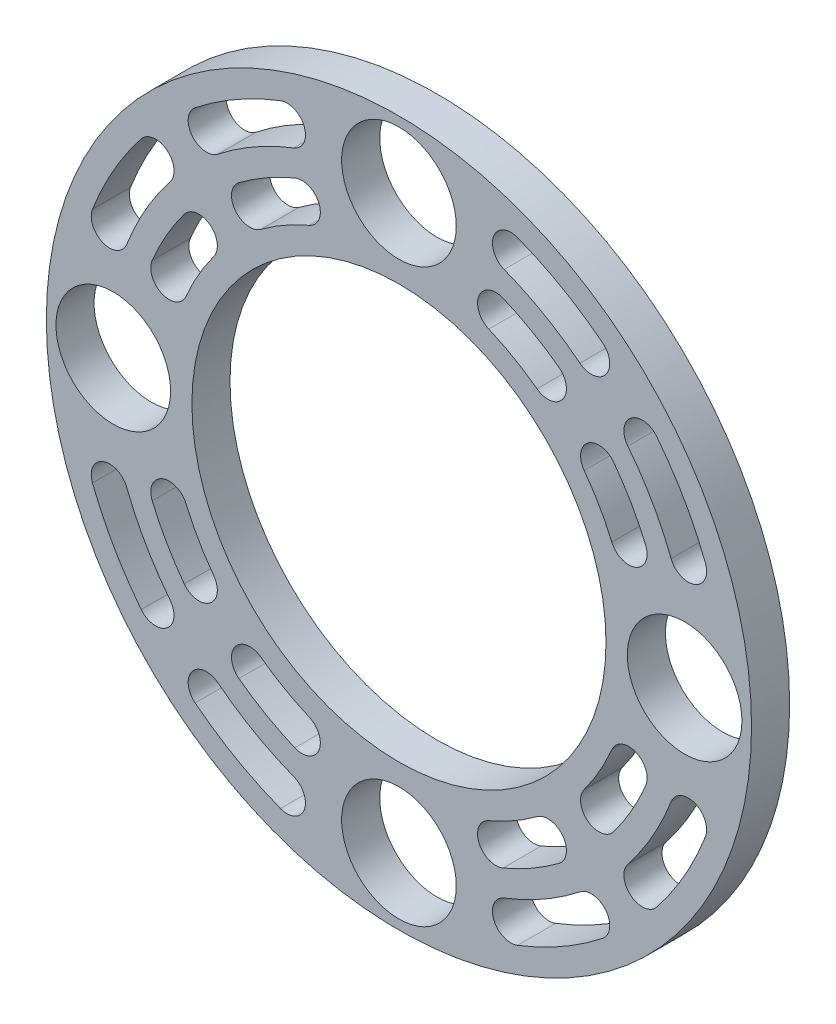
SolidWorks part; units mm, degrees
material "6061-T6 (SS)"
ref_plane "Front Plane" through (0, 0, 0) normal (0, 0, 1) x (1, 0, 0)
ref_plane "Top Plane" through (0, 0, 0) normal (0, 1, 0) x (1, 0, 0)
ref_plane "Right Plane" through (0, 0, 0) normal (1, 0, 0) x (0, 0, -1)
sketch "Sketch6" plane through (0, 0, 0) normal (0, 0, 1) x (1, 0, 0)
  circle A0 centre (0, 0) radius 34.5
  circle A1 centre (0, 0) radius 58.75
  dimension "D1" = 117.5
  dimension "D2" = 69
extrude "Boss-Extrude1" add sketch "Sketch6" along normal blind 6.35
sketch "Sketch5" plane through (0, 0, 0) normal (0, 0, 1) x (1, 0, 0)
  circle A0 centre (0, 47.6) radius 9.55
  circle A1 centre (47.6, 0) radius 9.55
  circle A2 centre (0, -47.6) radius 9.55
  circle A3 centre (-47.6, 0) radius 9.55
  point P12 (0, 0)
  dimension "D1" = 19.1
  dimension "D2" = 47.6
extrude "Cut-Extrude1" cut sketch "Sketch5" along normal through all
sketch "Sketch9" plane through (0, 0, 0) normal (0, 0, 1) x (1, 0, 0)
  line L0 (0, 0) -> (0, 47.6) construction
  line L1 (0, 0) -> (41.5425, 41.5425) construction
  line L2 (0, 0) -> (29.1406, 51.0136) construction
  line L3 (32.0589, 40.5441) -> (36.3015, 36.3015) construction
  line L4 (36.3015, 36.3015) -> (40.5441, 32.0589) construction
  line L5 (24.8386, 33.3239) -> (29.0813, 29.0813) construction
  line L6 (29.0813, 29.0813) -> (33.3239, 24.8386) construction
  line L7 (18.64, 48.2094) -> (0, 47.6) construction
  line L8 (0, 47.6) -> (16.1611, 38.2918) construction
  line L9 (0, 0) -> (-47.6, 0) construction
  arc A0 (18.64, 48.2094) -> (32.0589, 40.5441) centre (0, 0) cw construction
  arc A1 (33.9584, 42.9464) -> (19.7445, 51.0658) centre (0, 0) ccw
  arc A2 (30.1594, 38.1419) -> (17.5356, 45.353) centre (0, 0) ccw
  arc A3 (30.1594, 38.1419) -> (33.9584, 42.9464) centre (32.0589, 40.5441) ccw
  arc A4 (19.7445, 51.0658) -> (17.5356, 45.353) centre (18.64, 48.2094) ccw
  arc A5 (40.5441, 32.0589) -> (48.2094, 18.64) centre (0, 0) cw construction
  arc A6 (51.0658, 19.7445) -> (42.9464, 33.9584) centre (0, 0) ccw
  arc A7 (45.353, 17.5356) -> (38.1419, 30.1594) centre (0, 0) ccw
  arc A8 (45.353, 17.5356) -> (51.0658, 19.7445) centre (48.2094, 18.64) ccw
  arc A9 (42.9464, 33.9584) -> (38.1419, 30.1594) centre (40.5441, 32.0589) ccw
  circle A10 centre (0, 0) radius 58.75 construction
  circle A11 centre (0, 0) radius 58.75 construction
  arc A12 (16.1611, 38.2918) -> (24.8386, 33.3239) centre (0, 0) cw construction
  arc A13 (26.6689, 35.7794) -> (17.3519, 41.1133) centre (0, 0) ccw
  arc A14 (23.0084, 30.8685) -> (14.9702, 35.4703) centre (0, 0) ccw
  arc A15 (23.0084, 30.8685) -> (26.6689, 35.7794) centre (24.8386, 33.3239) ccw
  arc A16 (17.3519, 41.1133) -> (14.9702, 35.4703) centre (16.1611, 38.2918) ccw
  arc A17 (33.3239, 24.8386) -> (38.2918, 16.1611) centre (0, 0) cw construction
  arc A18 (41.1133, 17.3519) -> (35.7794, 26.6689) centre (0, 0) ccw
  arc A19 (35.4703, 14.9702) -> (30.8685, 23.0084) centre (0, 0) ccw
  arc A20 (35.4703, 14.9702) -> (41.1133, 17.3519) centre (38.2918, 16.1611) ccw
  arc A21 (35.7794, 26.6689) -> (30.8685, 23.0084) centre (33.3239, 24.8386) ccw
  circle A22 centre (0, 0) radius 34.5 construction
  arc A23 (-18.64, 48.2094) -> (-32.0589, 40.5441) centre (0, 0) ccw construction
  arc A24 (-33.9584, 42.9464) -> (-19.7445, 51.0658) centre (0, 0) cw
  arc A25 (-30.1594, 38.1419) -> (-17.5356, 45.353) centre (0, 0) cw
  arc A26 (-30.1594, 38.1419) -> (-33.9584, 42.9464) centre (-32.0589, 40.5441) cw
  arc A27 (-19.7445, 51.0658) -> (-17.5356, 45.353) centre (-18.64, 48.2094) cw
  arc A28 (-40.5441, 32.0589) -> (-48.2094, 18.64) centre (0, 0) ccw construction
  arc A29 (-51.0658, 19.7445) -> (-42.9464, 33.9584) centre (0, 0) cw
  arc A30 (-45.353, 17.5356) -> (-38.1419, 30.1594) centre (0, 0) cw
  arc A31 (-45.353, 17.5356) -> (-51.0658, 19.7445) centre (-48.2094, 18.64) cw
  arc A32 (-42.9464, 33.9584) -> (-38.1419, 30.1594) centre (-40.5441, 32.0589) cw
  arc A33 (-16.1611, 38.2918) -> (-24.8386, 33.3239) centre (0, 0) ccw construction
  arc A34 (-26.6689, 35.7794) -> (-17.3519, 41.1133) centre (0, 0) cw
  arc A35 (-23.0084, 30.8685) -> (-14.9702, 35.4703) centre (0, 0) cw
  arc A36 (-23.0084, 30.8685) -> (-26.6689, 35.7794) centre (-24.8386, 33.3239) cw
  arc A37 (-17.3519, 41.1133) -> (-14.9702, 35.4703) centre (-16.1611, 38.2918) cw
  arc A38 (-33.3239, 24.8386) -> (-38.2918, 16.1611) centre (0, 0) ccw construction
  arc A39 (-41.1133, 17.3519) -> (-35.7794, 26.6689) centre (0, 0) cw
  arc A40 (-35.4703, 14.9702) -> (-30.8685, 23.0084) centre (0, 0) cw
  arc A41 (-35.4703, 14.9702) -> (-41.1133, 17.3519) centre (-38.2918, 16.1611) cw
  arc A42 (-35.7794, 26.6689) -> (-30.8685, 23.0084) centre (-33.3239, 24.8386) cw
  arc A43 (-18.64, -48.2094) -> (-32.0589, -40.5441) centre (0, 0) cw construction
  arc A44 (-33.9584, -42.9464) -> (-19.7445, -51.0658) centre (0, 0) ccw
  arc A45 (-30.1594, -38.1419) -> (-17.5356, -45.353) centre (0, 0) ccw
  arc A46 (-30.1594, -38.1419) -> (-33.9584, -42.9464) centre (-32.0589, -40.5441) ccw
  arc A47 (-19.7445, -51.0658) -> (-17.5356, -45.353) centre (-18.64, -48.2094) ccw
  arc A48 (-40.5441, -32.0589) -> (-48.2094, -18.64) centre (0, 0) cw construction
  arc A49 (-51.0658, -19.7445) -> (-42.9464, -33.9584) centre (0, 0) ccw
  arc A50 (-45.353, -17.5356) -> (-38.1419, -30.1594) centre (0, 0) ccw
  arc A51 (-45.353, -17.5356) -> (-51.0658, -19.7445) centre (-48.2094, -18.64) ccw
  arc A52 (-42.9464, -33.9584) -> (-38.1419, -30.1594) centre (-40.5441, -32.0589) ccw
  arc A53 (-16.1611, -38.2918) -> (-24.8386, -33.3239) centre (0, 0) cw construction
  arc A54 (-26.6689, -35.7794) -> (-17.3519, -41.1133) centre (0, 0) ccw
  arc A55 (-23.0084, -30.8685) -> (-14.9702, -35.4703) centre (0, 0) ccw
  arc A56 (-23.0084, -30.8685) -> (-26.6689, -35.7794) centre (-24.8386, -33.3239) ccw
  arc A57 (-17.3519, -41.1133) -> (-14.9702, -35.4703) centre (-16.1611, -38.2918) ccw
  arc A58 (-33.3239, -24.8386) -> (-38.2918, -16.1611) centre (0, 0) cw construction
  arc A59 (-41.1133, -17.3519) -> (-35.7794, -26.6689) centre (0, 0) ccw
  arc A60 (-35.4703, -14.9702) -> (-30.8685, -23.0084) centre (0, 0) ccw
  arc A61 (-35.4703, -14.9702) -> (-41.1133, -17.3519) centre (-38.2918, -16.1611) ccw
  arc A62 (-35.7794, -26.6689) -> (-30.8685, -23.0084) centre (-33.3239, -24.8386) ccw
  arc A63 (18.64, -48.2094) -> (32.0589, -40.5441) centre (0, 0) ccw construction
  arc A64 (33.9584, -42.9464) -> (19.7445, -51.0658) centre (0, 0) cw
  arc A65 (30.1594, -38.1419) -> (17.5356, -45.353) centre (0, 0) cw
  arc A66 (30.1594, -38.1419) -> (33.9584, -42.9464) centre (32.0589, -40.5441) cw
  arc A67 (19.7445, -51.0658) -> (17.5356, -45.353) centre (18.64, -48.2094) cw
  arc A68 (16.1611, -38.2918) -> (24.8386, -33.3239) centre (0, 0) ccw construction
  arc A69 (26.6689, -35.7794) -> (17.3519, -41.1133) centre (0, 0) cw
  arc A70 (23.0084, -30.8685) -> (14.9702, -35.4703) centre (0, 0) cw
  arc A71 (23.0084, -30.8685) -> (26.6689, -35.7794) centre (24.8386, -33.3239) cw
  arc A72 (17.3519, -41.1133) -> (14.9702, -35.4703) centre (16.1611, -38.2918) cw
  arc A73 (33.3239, -24.8386) -> (38.2918, -16.1611) centre (0, 0) ccw construction
  arc A74 (41.1133, -17.3519) -> (35.7794, -26.6689) centre (0, 0) cw
  arc A75 (35.4703, -14.9702) -> (30.8685, -23.0084) centre (0, 0) cw
  arc A76 (35.4703, -14.9702) -> (41.1133, -17.3519) centre (38.2918, -16.1611) cw
  arc A77 (35.7794, -26.6689) -> (30.8685, -23.0084) centre (33.3239, -24.8386) cw
  arc A78 (40.5441, -32.0589) -> (48.2094, -18.64) centre (0, 0) ccw construction
  arc A79 (51.0658, -19.7445) -> (42.9464, -33.9584) centre (0, 0) cw
  arc A80 (45.353, -17.5356) -> (38.1419, -30.1594) centre (0, 0) cw
  arc A81 (45.353, -17.5356) -> (51.0658, -19.7445) centre (48.2094, -18.64) cw
  arc A82 (42.9464, -33.9584) -> (38.1419, -30.1594) centre (40.5441, -32.0589) cw
  point P6 (25.6375, 44.8811)
  point P14 (44.8811, 25.6375)
  point P32 (20.6498, 36.0698)
  point P37 (36.0698, 20.6498)
  point P54 (-25.6375, 44.8811)
  point P61 (-44.8811, 25.6375)
  point P68 (-20.6498, 36.0698)
  point P75 (-36.0698, 20.6498)
  point P85 (-25.6375, -44.8811)
  point P92 (-44.8811, -25.6375)
  point P99 (-20.6498, -36.0698)
  point P106 (-36.0698, -20.6498)
  point P113 (25.6375, -44.8811)
  point P120 (20.6498, -36.0698)
  point P127 (36.0698, -20.6498)
  point P134 (44.8811, -25.6375)
  dimension "D1" = 45
  dimension "D2" = 4
  dimension "D5" = 3.0625
  dimension "D6" = 12
  dimension "D7" = 12
  dimension "D3" = 4
  dimension "D4" = 4
  dimension "D8" = 18.65
extrude "Cut-Extrude3" cut sketch "Sketch9" along normal through all
